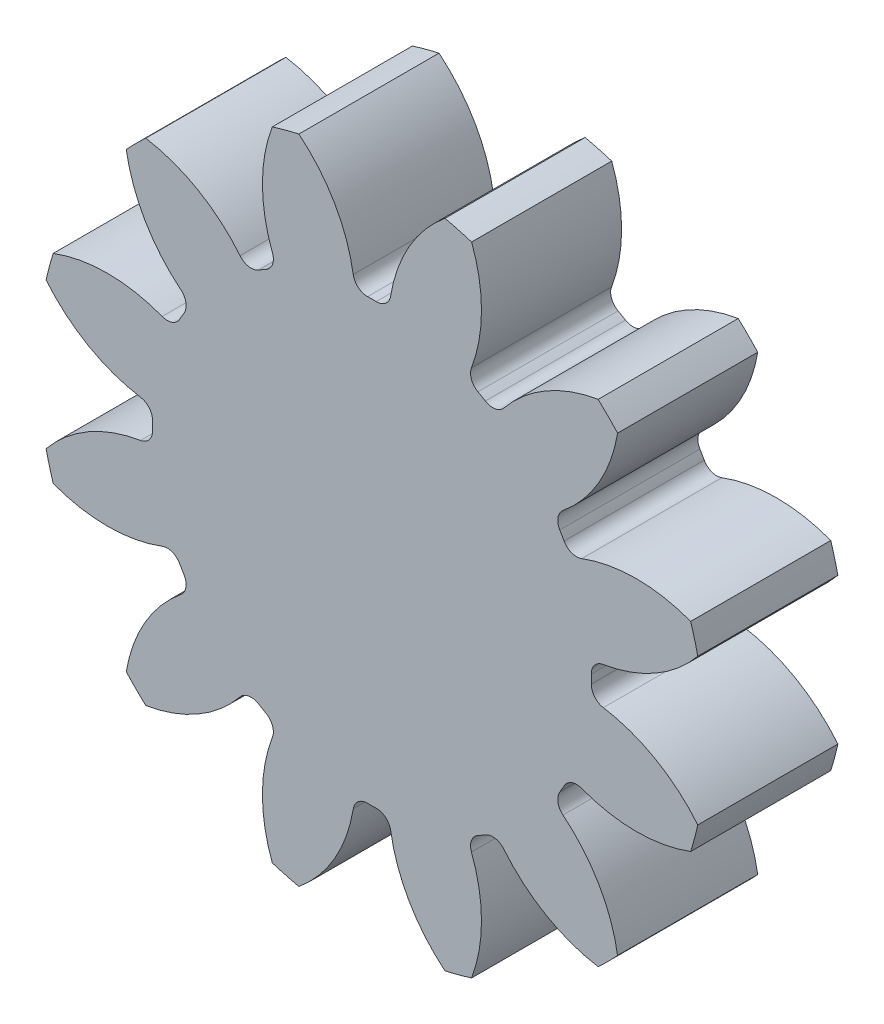
SolidWorks part; units mm, degrees
ref_plane "Front" through (0, 0, 0) normal (0, 0, 1) x (1, 0, 0)
ref_plane "Top" through (0, 0, 0) normal (0, 1, 0) x (1, 0, 0)
ref_plane "Right" through (0, 0, 0) normal (1, 0, 0) x (0, 0, -1)
sketch "Sketch2" plane through (0, 0, 0) normal (0, 0, 1) x (1, 0, 0)
  circle A0 centre (0, 0) radius 4.6986
  circle A1 centre (0, 0) radius 6.1286
  circle A2 centre (0, 0) radius 7.15
  dimension "D1" = 12.2571
  dimension "D2" = 14.3
  dimension "D3" = 2.4514
extrude "Boss-Extrude1" add sketch "Sketch2" along normal mid plane 3 contours A2
sketch "Sketch3" plane through (0, 0, 0) normal (0, 0, 1) x (1, 0, 0)
  line L0 (0, 0) -> (0, 7.15) construction
  line L1 (-0.7999, 6.0761) -> (0.7999, 6.0761) construction
  line L2 (0, 0) -> (-0.3678, 4.6842) construction
  line L3 (0, 4.6906) -> (-1.8715, 7.9322) construction
  line L4 (0, 0) -> (1.8506, 6.9064) construction
  line L5 (0.7999, 6.0761) -> (2.3453, 5.6621) construction
  circle A0 centre (0, 0) radius 7.15 construction
  arc A1 (-0.3678, 4.6842) -> (-2.8651, 7.6298) centre (-3.6585, 4.4257) ccw
  arc A2 (0.3678, 4.6842) -> (2.8651, 7.6298) centre (3.6585, 4.4257) cw
  circle A3 centre (0, 0) radius 4.6986 construction
  arc A4 (0.3678, 4.6842) -> (-0.3678, 4.6842) centre (0, 0) ccw
  circle A6 centre (0, 0) radius 6.1286 construction
  circle A7 centre (0, 0) radius 8.15
  arc A8 (2.8651, 7.6298) -> (-2.8651, 7.6298) centre (0, 0) ccw
  circle A9 centre (0, 0) radius 7.15 construction
  dimension "D2" = 30
  dimension "D3" = 15
  dimension "D1" = 1
extrude "Cut-Extrude1" cut sketch "Sketch3" against normal through all both and the other way through all contours A8 A1 A4 A2
fillet "Fillet1" radius 0.3064 2 edges at (0.3678, 4.6842, 0) (-0.3678, 4.6842, 0)
pattern_circular "CirPattern1" count 12 over 360 about axis through (0, 0, 0) along (0, 0, 1) of "Fillet1", "Cut-Extrude1"
equation "\"teeth\"= 12"
equation "\"module\"= ( 12.3 + 2 ) / ( \"teeth\" + 2 )"
equation "\"D1@Sketch2\"=\"module\"*\"teeth\""
equation "\"D2@Sketch2\"=(\"teeth\"+2)*\"module\""
equation "\"pressure_angle\"= 30deg"
equation "\"D2@Sketch3\"=\"pressure_angle\""
equation "\"D3@Sketch3\"=180/\"teeth\""
equation "\"D1@Fillet1\"=0.3 * \"module\""
equation "\"D1@CirPattern1\"=\"teeth\""
equation "\"D3@Sketch2\"=\"module\" * if ( \"module\" >= 1.25 , 2.25 , 2.4 )"
